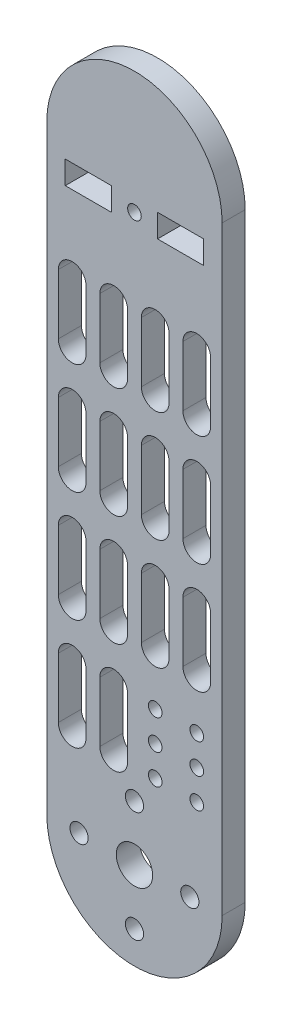
SolidWorks part; units mm, degrees
ref_plane "Front Plane" through (0, 0, 0) normal (0, 0, 1) x (1, 0, 0)
ref_plane "Top Plane" through (0, 0, 0) normal (0, 1, 0) x (1, 0, 0)
ref_plane "Right Plane" through (0, 0, 0) normal (1, 0, 0) x (0, 0, -1)
sketch "Sketch1" plane through (0, 0, 0) normal (0, 0, 1) x (1, 0, 0)
  line L0 (0, 12) -> (0, 0) construction
  line L1 (0, 0) -> (19, 0) construction
  line L2 (-19, 0) -> (-19, 130)
  line L3 (19, 0) -> (19, 130)
  line L4 (-19, 130) -> (19, 130) construction
  line L5 (4.5, 103.5) -> (4.5, 90.5) construction
  line L6 (7.5, 103.5) -> (7.5, 90.5)
  line L7 (1.5, 103.5) -> (1.5, 90.5)
  line L8 (-4.5, 103.5) -> (-4.5, 90.5) construction
  line L9 (-7.5, 103.5) -> (-7.5, 90.5)
  line L10 (-1.5, 103.5) -> (-1.5, 90.5)
  line L11 (13.5, 103.5) -> (13.5, 90.5) construction
  line L12 (16.5, 103.5) -> (16.5, 90.5)
  line L13 (10.5, 103.5) -> (10.5, 90.5)
  line L14 (-13.5, 103.5) -> (-13.5, 90.5) construction
  line L15 (-16.5, 103.5) -> (-16.5, 90.5)
  line L16 (-10.5, 103.5) -> (-10.5, 90.5)
  line L17 (4.5, 79.5) -> (4.5, 66.5) construction
  line L18 (7.5, 79.5) -> (7.5, 66.5)
  line L19 (1.5, 79.5) -> (1.5, 66.5)
  line L20 (-4.5, 79.5) -> (-4.5, 66.5) construction
  line L21 (-7.5, 79.5) -> (-7.5, 66.5)
  line L22 (-1.5, 79.5) -> (-1.5, 66.5)
  line L23 (13.5, 79.5) -> (13.5, 66.5) construction
  line L24 (16.5, 79.5) -> (16.5, 66.5)
  line L25 (10.5, 79.5) -> (10.5, 66.5)
  line L26 (-13.5, 79.5) -> (-13.5, 66.5) construction
  line L27 (-16.5, 79.5) -> (-16.5, 66.5)
  line L28 (-10.5, 79.5) -> (-10.5, 66.5)
  line L29 (4.5, 55.5) -> (4.5, 42.5) construction
  line L30 (7.5, 55.5) -> (7.5, 42.5)
  line L31 (1.5, 55.5) -> (1.5, 42.5)
  line L32 (-4.5, 55.5) -> (-4.5, 42.5) construction
  line L33 (-7.5, 55.5) -> (-7.5, 42.5)
  line L34 (-1.5, 55.5) -> (-1.5, 42.5)
  line L35 (13.5, 55.5) -> (13.5, 42.5) construction
  line L36 (16.5, 55.5) -> (16.5, 42.5)
  line L37 (10.5, 55.5) -> (10.5, 42.5)
  line L38 (-13.5, 55.5) -> (-13.5, 42.5) construction
  line L39 (-16.5, 55.5) -> (-16.5, 42.5)
  line L40 (-10.5, 55.5) -> (-10.5, 42.5)
  line L44 (-4.5, 31.5) -> (-4.5, 18.5) construction
  line L45 (-7.5, 31.5) -> (-7.5, 18.5)
  line L46 (-1.5, 31.5) -> (-1.5, 18.5)
  line L50 (-13.5, 31.5) -> (-13.5, 18.5) construction
  line L51 (-16.5, 31.5) -> (-16.5, 18.5)
  line L52 (-10.5, 31.5) -> (-10.5, 18.5)
  line L63 (-15, 130) -> (-5, 130) construction
  line L67 (-19, 122.5) -> (19, 122.5) construction
  line L68 (15, 120) -> (5, 120)
  line L69 (-15, 125) -> (-5, 125)
  line L70 (-15, 125) -> (-15, 120)
  line L71 (-15, 120) -> (-5, 120)
  line L72 (-5, 125) -> (-5, 120)
  line L73 (-10, 120) -> (-10, 125) construction
  line L74 (-15, 122.5) -> (-5, 122.5) construction
  line L75 (5, 125) -> (5, 120)
  line L76 (15, 125) -> (5, 125)
  line L77 (15, 125) -> (15, 120)
  line L78 (13.5, 31.5) -> (13.5, 18.5) construction
  line L79 (16.5, 31.5) -> (16.5, 18.5) [skipped]
  line L80 (10.5, 31.5) -> (10.5, 18.5) [skipped]
  line L81 (4.5, 31.5) -> (4.5, 18.5) construction
  line L82 (7.5, 31.5) -> (7.5, 18.5) [skipped]
  line L83 (1.5, 31.5) -> (1.5, 18.5) [skipped]
  line L84 (13.5, 31.5) -> (13.5, 18.5) construction
  line L85 (16.5, 31.5) -> (16.5, 18.5) [skipped]
  line L86 (10.5, 31.5) -> (10.5, 18.5) [skipped]
  line L87 (4.5, 31.5) -> (4.5, 18.5) construction
  line L88 (7.5, 31.5) -> (7.5, 18.5) [skipped]
  line L89 (1.5, 31.5) -> (1.5, 18.5) [skipped]
  circle A0 centre (0, 0) radius 3.95
  arc A1 (-19, 0) -> (19, 0) centre (0, 0) ccw
  circle A2 centre (0, 12) radius 1.975
  circle A3 centre (12, 0) radius 1.975
  circle A4 centre (0, -12) radius 1.975
  circle A5 centre (-12, 0) radius 1.975
  arc A6 (19, 130) -> (-19, 130) centre (0, 130) ccw
  circle A7 centre (13.5, 25) radius 1.475
  arc A8 (7.5, 103.5) -> (1.5, 103.5) centre (4.5, 103.5) ccw
  arc A9 (1.5, 90.5) -> (7.5, 90.5) centre (4.5, 90.5) ccw
  arc A10 (-7.5, 103.5) -> (-1.5, 103.5) centre (-4.5, 103.5) cw
  arc A11 (-1.5, 90.5) -> (-7.5, 90.5) centre (-4.5, 90.5) cw
  arc A12 (16.5, 103.5) -> (10.5, 103.5) centre (13.5, 103.5) ccw
  arc A13 (10.5, 90.5) -> (16.5, 90.5) centre (13.5, 90.5) ccw
  arc A14 (-16.5, 103.5) -> (-10.5, 103.5) centre (-13.5, 103.5) cw
  arc A15 (-10.5, 90.5) -> (-16.5, 90.5) centre (-13.5, 90.5) cw
  arc A16 (7.5, 79.5) -> (1.5, 79.5) centre (4.5, 79.5) ccw
  arc A17 (1.5, 66.5) -> (7.5, 66.5) centre (4.5, 66.5) ccw
  arc A18 (-7.5, 79.5) -> (-1.5, 79.5) centre (-4.5, 79.5) cw
  arc A19 (-1.5, 66.5) -> (-7.5, 66.5) centre (-4.5, 66.5) cw
  arc A20 (16.5, 79.5) -> (10.5, 79.5) centre (13.5, 79.5) ccw
  arc A21 (10.5, 66.5) -> (16.5, 66.5) centre (13.5, 66.5) ccw
  arc A22 (-16.5, 79.5) -> (-10.5, 79.5) centre (-13.5, 79.5) cw
  arc A23 (-10.5, 66.5) -> (-16.5, 66.5) centre (-13.5, 66.5) cw
  arc A24 (7.5, 55.5) -> (1.5, 55.5) centre (4.5, 55.5) ccw
  arc A25 (1.5, 42.5) -> (7.5, 42.5) centre (4.5, 42.5) ccw
  arc A26 (-7.5, 55.5) -> (-1.5, 55.5) centre (-4.5, 55.5) cw
  arc A27 (-1.5, 42.5) -> (-7.5, 42.5) centre (-4.5, 42.5) cw
  arc A28 (16.5, 55.5) -> (10.5, 55.5) centre (13.5, 55.5) ccw
  arc A29 (10.5, 42.5) -> (16.5, 42.5) centre (13.5, 42.5) ccw
  arc A30 (-16.5, 55.5) -> (-10.5, 55.5) centre (-13.5, 55.5) cw
  arc A31 (-10.5, 42.5) -> (-16.5, 42.5) centre (-13.5, 42.5) cw
  arc A34 (-7.5, 31.5) -> (-1.5, 31.5) centre (-4.5, 31.5) cw
  arc A35 (-1.5, 18.5) -> (-7.5, 18.5) centre (-4.5, 18.5) cw
  arc A38 (-16.5, 31.5) -> (-10.5, 31.5) centre (-13.5, 31.5) cw
  arc A39 (-10.5, 18.5) -> (-16.5, 18.5) centre (-13.5, 18.5) cw
  circle A44 centre (4.5, 25) radius 1.475
  circle A45 centre (13.5, 31.5) radius 1.475
  circle A46 centre (4.5, 31.5) radius 1.475
  circle A47 centre (13.5, 18.5) radius 1.475
  circle A48 centre (4.5, 18.5) radius 1.475
  circle A51 centre (0, 122.5) radius 1.475
  arc A56 (16.5, 31.5) -> (10.5, 31.5) centre (13.5, 31.5) ccw [skipped]
  arc A57 (10.5, 18.5) -> (16.5, 18.5) centre (13.5, 18.5) ccw [skipped]
  arc A58 (7.5, 31.5) -> (1.5, 31.5) centre (4.5, 31.5) ccw [skipped]
  arc A59 (1.5, 18.5) -> (7.5, 18.5) centre (4.5, 18.5) ccw [skipped]
  point P19 (0, 0)
  point P22 (4.5, 97)
  point P29 (-4.5, 97)
  point P36 (13.5, 97)
  point P43 (-13.5, 97)
  point P52 (4.5, 73)
  point P59 (-4.5, 73)
  point P66 (13.5, 73)
  point P73 (-13.5, 73)
  point P80 (4.5, 49)
  point P87 (-4.5, 49)
  point P94 (13.5, 49)
  point P101 (-13.5, 49)
  point P108 (13.5, 25)
  point P115 (-4.5, 25)
  point P122 (-10, 130)
  point P129 (-13.5, 25)
  point P136 (4.5, 25)
  point P149 (-10, 122.5)
  point P419 (13.5, 25)
  point P426 (4.5, 25)
  point P433 (13.5, 25)
  point P440 (4.5, 25)
  dimension "D1" = 7.9
  dimension "D2" = 38
  dimension "D3" = 3.95
  dimension "D8" = 38
  dimension "D9" = 2.95
  dimension "D14" = 4.5
  dimension "D15" = 26.5
  dimension "D17" = 3
  dimension "D20" = 4
  dimension "D13" = 3
  dimension "D23" = 2
  dimension "D30" = 2.95
  dimension "D4" = 12
  dimension "D5" = 4
  dimension "D6" = 130
  dimension "D7" = 130
  dimension "D10" = 25
  dimension "D11" = 13.5
  dimension "D12" = 13
  dimension "D16" = 13
  dimension "D18" = 26.5
  dimension "D19" = 9
  dimension "D21" = 11
  dimension "D22" = 2
  dimension "D29" = 7.5
  dimension "D31" = 10
  dimension "D32" = 5
  dimension "D33" = 10
  dimension "D24" = 2
extrude "Boss-Extrude1" add sketch "Sketch1" along normal blind 5 contours L3 A6 L2 A1 A51 A48 A47 A46 A45 A44 A29 L37 A28 L36 A25 L31 A24 L30 A21 L25 A20 L24 A17 L19 A16 L18 A13 L13 A12 L12 A9 L7 A8 L6 A7 L76 L77
